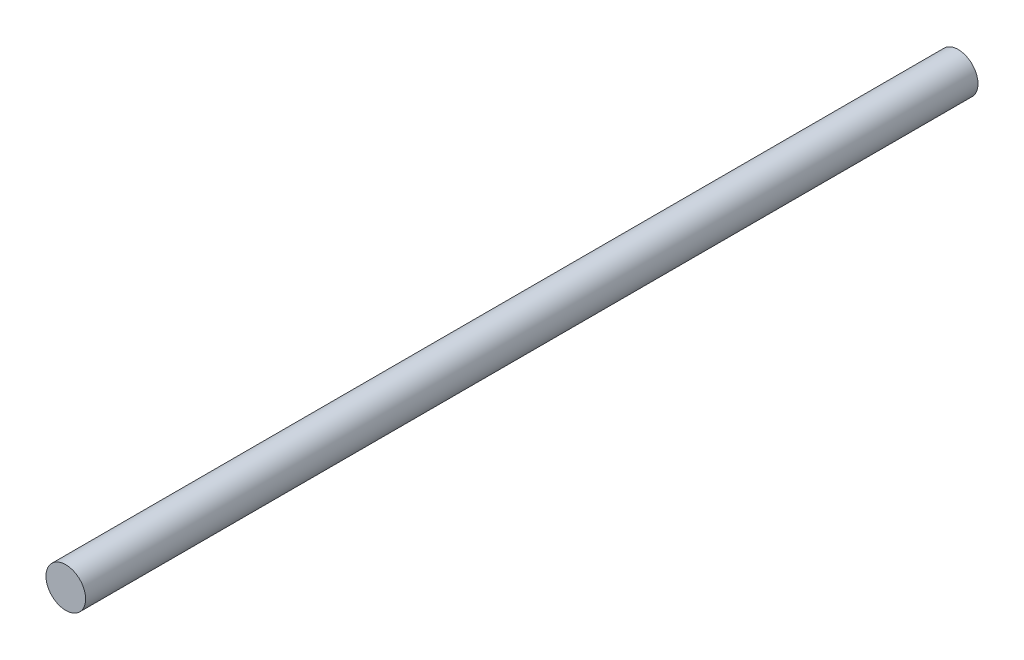
SolidWorks part; units mm, degrees
ref_plane "前视基准面" through (0, 0, 0) normal (0, 0, 1) x (1, 0, 0)
ref_plane "上视基准面" through (0, 0, 0) normal (0, 1, 0) x (1, 0, 0)
ref_plane "右视基准面" through (0, 0, 0) normal (1, 0, 0) x (0, 0, -1)
other "Configuration Table"
sketch "草图1" plane through (0, 0, 0) normal (0, 0, 1) x (1, 0, 0)
  circle A0 centre (0, 0) radius 2
extrude "凸台-拉伸1" add sketch "草图1" along normal blind 90
